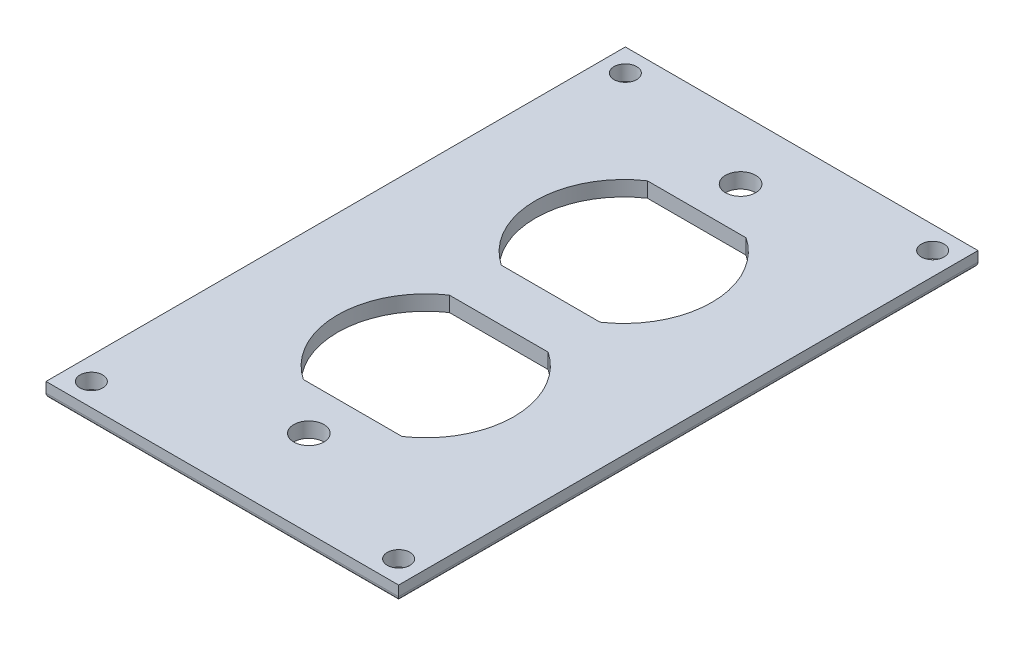
SolidWorks part; units mm, degrees
ref_plane "Front Plane" through (0, 0, 0) normal (0, 0, 1) x (1, 0, 0)
ref_plane "Top Plane" through (0, 0, 0) normal (0, 1, 0) x (1, 0, 0)
ref_plane "Right Plane" through (0, 0, 0) normal (1, 0, 0) x (0, 0, -1)
sketch "Sketch1" plane through (0, 0, 0) normal (0, 1, 0) x (1, 0, 0)
  line L1 (-35, 57.5) -> (35, 57.5)
  line L2 (-35, 57.5) -> (-35, -57.5)
  line L3 (-35, -57.5) -> (35, -57.5)
  line L4 (35, 57.5) -> (35, -57.5)
  line L5 (-35, 57.5) -> (35, -57.5) construction
  line L6 (-35, -57.5) -> (35, 57.5) construction
  point P0 (0, 0)
  dimension "D1" = 70
  dimension "D2" = 115
extrude "Boss-Extrude1" add sketch "Sketch1" along normal blind 3
sketch "Sketch4" plane through (0, 0, 0) normal (0, -1, 0) x (-1, 0, 0)
  line L0 (35, -57.5) -> (-35, -57.5) construction
  line L2 (35, 57.5) -> (35, -57.5) construction
  circle A0 centre (30.5, -53) radius 2.25
  dimension "D1" = 4.5
  dimension "D2" = 4.5
  dimension "D3" = 4.5
extrude "Cut-Extrude2" cut sketch "Sketch4" against normal blind 3
mirror "Mirror1" about plane through (0, 0, 0) normal (1, 0, 0) of "Cut-Extrude2" second plane through (0, 0, 0) second plane normal (0, 0, 1)
fillet "Fillet4" radius 1 4 edges at (0, 0, 57.5) (-35, 0, 0) (0, 0, -57.5) (35, 0, 0)
sketch "Sketch18" plane through (0, 0, 0) normal (0, -1, 0) x (-1, 0, 0)
  line L0 (0, -56.5) -> (0, 56.5) construction
  line L1 (-34, -56.5) -> (34, -56.5) construction
  line L2 (34, 56.5) -> (-34, 56.5) construction
  line L3 (35, 0) -> (5.7512, 0) construction
  line L4 (35, 57.5) -> (35, -57.5) construction
  line L6 (10, -31.625) -> (-10, -31.625)
  line L7 (10, -31.625) -> (-10, -31.625)
  line L9 (10, -2.625) -> (-10.25, -2.625)
  line L11 (17.5, -31.625) -> (-17.5, -2.625) construction
  line L12 (17.5, -2.625) -> (-17.5, -31.625) construction
  line L13 (10, -2.625) -> (-10.25, -2.625)
  line L14 (17.5, -17.125) -> (-17.5, -17.125) construction
  line L15 (0, -31.625) -> (17.5, -17.125) construction
  line L16 (17.5, -17.125) -> (0, -31.625) construction
  line L17 (0, -31.625) -> (-17.5, -17.125) construction
  line L18 (-17.5, -17.125) -> (0, -2.625) construction
  line L19 (0, -2.625) -> (17.5, -17.125) construction
  line L20 (-9.798, -2.625) -> (9.798, -2.625)
  arc A7 (-9.798, -2.625) -> (-9.798, -31.625) centre (0, -17.125) ccw
  arc A8 (9.798, -31.625) -> (9.798, -2.625) centre (0, -17.125) ccw
  point P12 (0, -17.125)
  dimension "D6" = 35
  dimension "D1" = 35
  dimension "D2" = 29
  dimension "D3" = 5.25
  dimension "D4" = 20
  dimension "D5" = 7.5
extrude "Cut-Extrude13" cut sketch "Sketch18" against normal blind 3 and the other way through all contours L7 A8 L13 A7
ref_plane "Plane1" through (0, 0, -2.525) normal (0, 0, 1) x (1, 0, 0)
mirror "Mirror3" about plane through (0, 0, -2.525) normal (0, 0, 1) of "Cut-Extrude13"
sketch "Sketch21" plane through (0, 3, 0) normal (0, 1, 0) x (1, 0, 0)
  line L0 (0, 57.5) -> (0, -57.5) construction
  line L1 (35, 57.5) -> (-35, 57.5) construction
  line L2 (-35, -57.5) -> (35, -57.5) construction
  line L3 (-9.798, -31.625) -> (9.798, -31.625) construction
  line L4 (-9.798, 36.675) -> (9.798, 36.675) construction
  circle A0 centre (0, 45.375) radius 3
  circle A1 centre (0, -40.325) radius 3
  point P10 (0, 0)
  dimension "D1" = 6
  dimension "D2" = 6
  dimension "D3" = 8.7
  dimension "D4" = 8.7
extrude "Cut-Extrude14" cut sketch "Sketch21" against normal blind 3
sketch "Sketch22" plane through (0, 3, 0) normal (0, 1, 0) x (1, 0, 0)
  line L0 (-35, 0) -> (35, 0) construction
  line L1 (-35, 57.5) -> (-35, -57.5) construction
  line L2 (35, -57.5) -> (35, 57.5) construction
